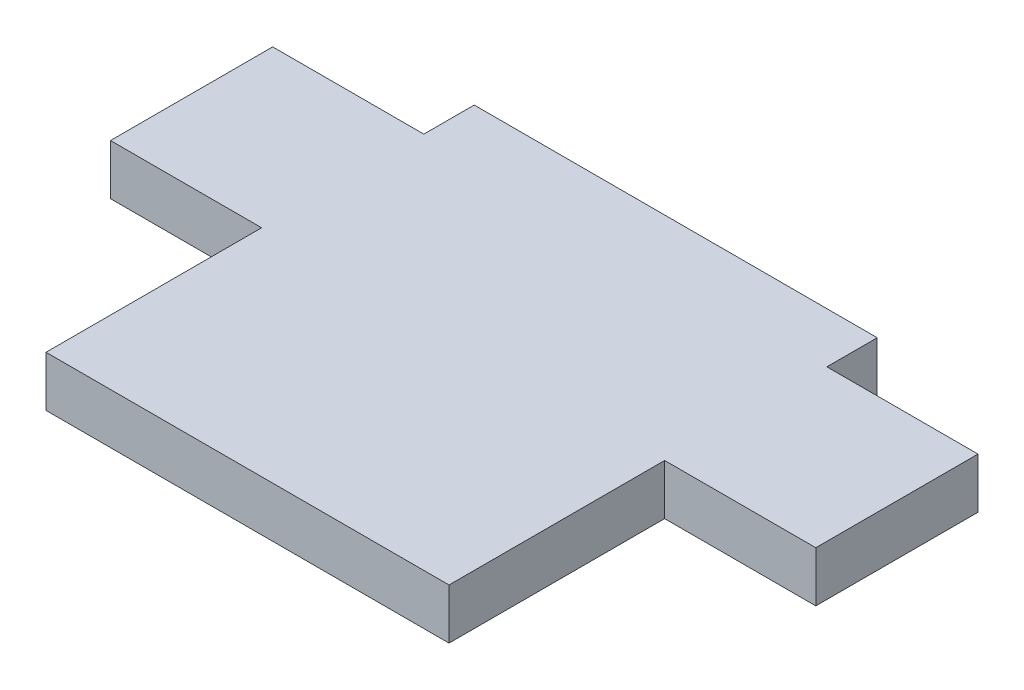
SolidWorks part; units mm, degrees
ref_plane "Front Plane" through (0, 0, 0) normal (0, 0, 1) x (1, 0, 0)
ref_plane "Top Plane" through (0, 0, 0) normal (0, 1, 0) x (1, 0, 0)
ref_plane "Right Plane" through (0, 0, 0) normal (1, 0, 0) x (0, 0, -1)
sketch "Sketch1" plane through (0, 0, 0) normal (0, 1, 0) x (1, 0, 0)
  line L0 (0, 13.3985) -> (-25.4, 13.3985)
  line L1 (-25.4, 13.3985) -> (-25.4, 10.2235)
  line L2 (-25.4, 10.2235) -> (-34.925, 10.2235)
  line L3 (-34.925, 10.2235) -> (-34.925, 0)
  line L4 (-34.925, 0) -> (-25.4, 0)
  line L5 (-25.4, 0) -> (-25.4, -13.589)
  line L6 (-25.4, -13.589) -> (0, -13.589)
  line L7 (0, -13.589) -> (0, 0)
  line L8 (0, 0) -> (9.525, 0)
  line L9 (9.525, 0) -> (9.525, 10.2235)
  line L10 (9.525, 10.2235) -> (0, 10.2235)
  line L11 (0, 10.2235) -> (0, 13.3985)
  dimension "D1" = 25.4
  dimension "D2" = 44.45
  dimension "D3" = 10.2235
  dimension "D4" = 3.175
  dimension "D5" = 13.589
extrude "Boss-Extrude1" add sketch "Sketch1" along normal blind 3.175
